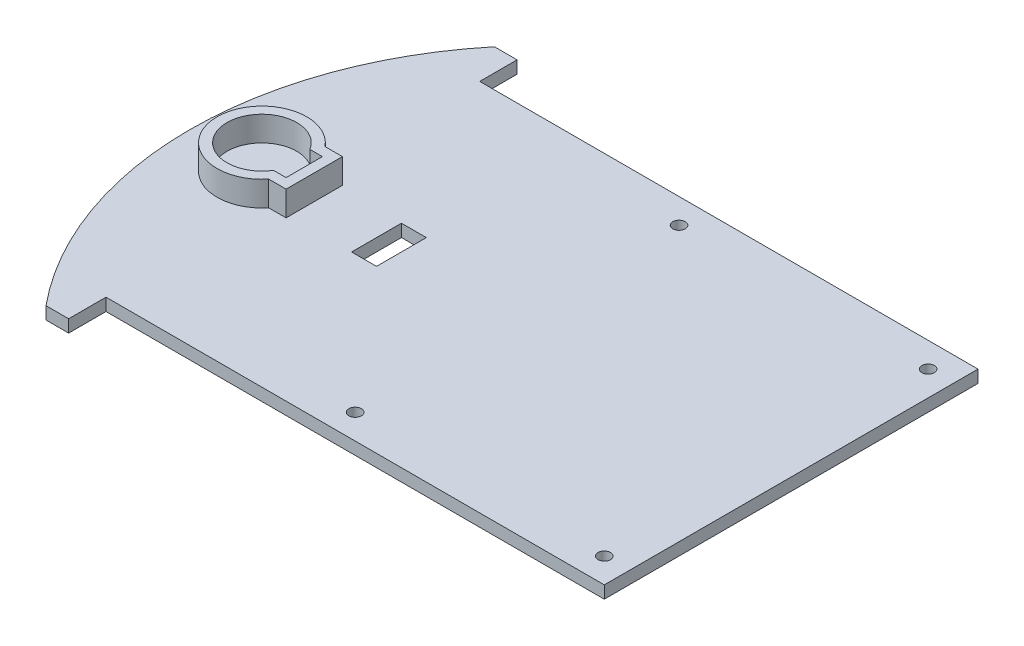
SolidWorks part; units mm, degrees
ref_plane "Alzado" through (0, 0, 0) normal (0, 0, 1) x (1, 0, 0)
ref_plane "Planta" through (0, 0, 0) normal (0, 1, 0) x (1, 0, 0)
ref_plane "Vista lateral" through (0, 0, 0) normal (1, 0, 0) x (0, 0, -1)
sketch "Croquis1" plane through (0, 0, 0) normal (0, 1, 0) x (1, 0, 0)
  line L0 (-71.2154, -85.3945) -> (-71.2154, -110.3945)
  line L1 (-71.2154, 64.6055) -> (128.7846, 64.6055)
  line L2 (-71.2154, 64.6055) -> (-71.2154, -85.3945)
  line L3 (-71.2154, -85.3945) -> (128.7846, -85.3945)
  line L4 (128.7846, 64.6055) -> (128.7846, -85.3945)
  line L5 (-71.2154, 64.6055) -> (-71.2154, 89.6055)
  line L6 (-71.2154, -10.3945) -> (-112.6367, -10.3945)
  line L7 (-71.2154, 79.6055) -> (-80.3025, 79.6055)
  line L8 (-71.2154, -100.3945) -> (-80.3025, -100.3945)
  arc A1 (-71.2154, -110.3945) -> (-71.2154, 89.6055) centre (28.7846, -10.3945) cw
  circle A2 centre (18.7846, -75.3945) radius 2.5
  circle A3 centre (18.7846, 54.6055) radius 2.5
  circle A4 centre (118.7846, 54.6055) radius 2.5
  circle A5 centre (118.7846, -75.3945) radius 2.5
  dimension "D6" = 5
  dimension "D7" = 5
  dimension "D8" = 5
  dimension "D9" = 5
  dimension "D1" = 200
  dimension "D2" = 150
  dimension "D3" = 25
  dimension "D4" = 25
  dimension "D5" = 41.4214
  dimension "D10" = 10
  dimension "D11" = 10
  dimension "D12" = 10
  dimension "D13" = 10
  dimension "D14" = 10
  dimension "D15" = 100
  dimension "D16" = 10
  dimension "D17" = 100
  dimension "D18" = 10
  dimension "D19" = 10
extrude "Saliente-Extruir1" add sketch "Croquis1" along normal blind 5 contours L4 L1 L2 L3 A5 A4 A3 A2 | A1 L0 L2 L6 | A1 L6 L2 L5
sketch "Croquis3" plane through (0, 5, 0) normal (0, 1, 0) x (1, 0, 0)
  line L0 (-83.6367, -10.3945) -> (-112.6367, -10.3945)
  line L1 (-79.3559, -17.6945) -> (-66.6367, -17.6945)
  line L2 (-79.3559, -17.6945) -> (-79.3559, -3.0945)
  line L3 (-79.3559, -3.0945) -> (-66.6367, -3.0945)
  line L4 (-66.6367, -17.6945) -> (-66.6367, -3.0945)
  line L5 (-79.3559, -17.6945) -> (-66.6367, -3.0945) construction
  line L6 (-79.3559, -3.0945) -> (-66.6367, -17.6945) construction
  line L7 (-83.3559, 0.9055) -> (-62.6367, 0.9055)
  line L8 (-83.6367, -10.3945) -> (-66.6367, -10.3945)
  line L9 (-62.6367, -21.6945) -> (-62.6367, 0.9055)
  line L10 (-83.3559, -21.6945) -> (-62.6367, -21.6945)
  line L11 (-83.3559, -21.6945) -> (-83.3559, 0.9055)
  circle A0 centre (-83.6367, -10.3945) radius 14
  arc A1 (-80.3025, 79.6055) -> (-80.3025, -100.3945) centre (28.7846, -10.3945) ccw construction
  circle A2 centre (-83.6367, -10.3945) radius 18
  point P2 (-72.9963, -10.3945)
  dimension "D2" = 28
  dimension "D4" = 29
  dimension "D1" = 14.6
  dimension "D3" = 17
  dimension "D5" = 4
extrude "Saliente-Extruir3" add sketch "Croquis3" along normal blind 10 contours L7 A2 L0 A0 | L0 A2 L10 A0 | L10 A2 L1 A0 | A2 L10 L9 L7 L3 L4 L1 | L4 A2 | L3 A2 L7 A0
sketch "Croquis4" plane through (0, 5, 0) normal (0, 1, 0) x (1, 0, 0)
  line L0 (-62.6367, -10.3945) -> (-32.6367, -10.3945)
  line L1 (-37.6367, -20.3945) -> (-27.6367, -20.3945)
  line L2 (-37.6367, -20.3945) -> (-37.6367, -0.3945)
  line L3 (-37.6367, -0.3945) -> (-27.6367, -0.3945)
  line L4 (-27.6367, -20.3945) -> (-27.6367, -0.3945)
  line L5 (-37.6367, -20.3945) -> (-27.6367, -0.3945) construction
  line L6 (-37.6367, -0.3945) -> (-27.6367, -20.3945) construction
  line L7 (-62.6367, -21.6945) -> (-62.6367, 0.9055) construction
  line L8 (-71.2154, -85.3945) -> (128.7846, -85.3945) construction
  line L9 (128.7846, 64.6055) -> (-21.2154, 64.6055)
  line L10 (128.7846, 64.6055) -> (128.7846, -85.3945)
  line L11 (128.7846, -85.3945) -> (-21.2154, -85.3945)
  line L12 (-21.2154, 64.6055) -> (-21.2154, -85.3945)
  point P0 (-32.6367, -10.3945)
  dimension "D1" = 20
  dimension "D2" = 10
  dimension "D3" = 25
  dimension "D4" = 150
extrude "Cortar-Extruir1" cut sketch "Croquis4" against normal blind 6
